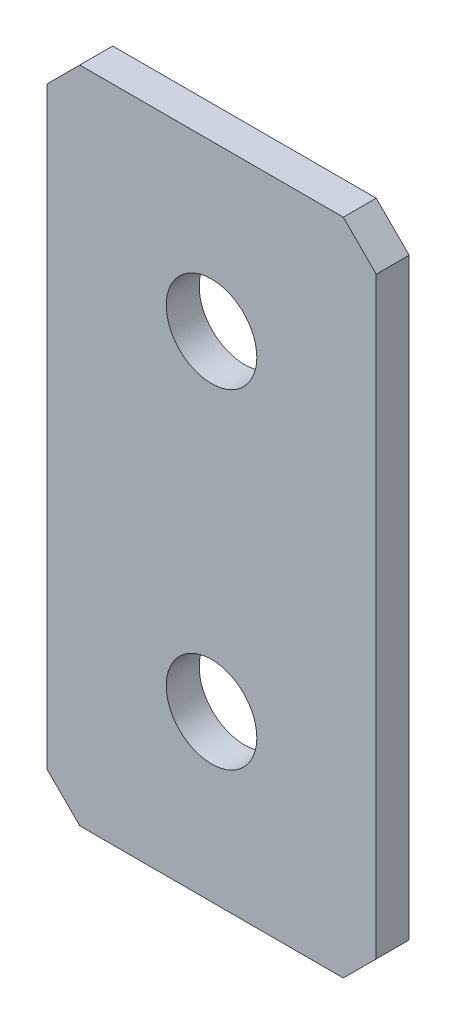
SolidWorks part; units mm, degrees
material "Простая углеродистая сталь"
ref_plane "Спереди(Плоскость XY)" through (0, 0, 0) normal (0, 0, 1) x (1, 0, 0)
ref_plane "Сверху(Плоскость XZ)" through (0, 0, 0) normal (0, 1, 0) x (1, 0, 0)
ref_plane "Справа(Плоскость ZY)" through (0, 0, 0) normal (1, 0, 0) x (0, 0, -1)
sketch "Эскиз1" plane through (0, 0, 0) normal (0, 0, 1) x (1, 0, 0)
  line L1 (-10, -20) -> (10, -20)
  line L2 (-10, -20) -> (-10, 20)
  line L3 (-10, 20) -> (10, 20)
  line L4 (10, -20) -> (10, 20)
  line L5 (-10, -20) -> (10, 20) construction
  line L6 (-10, 20) -> (10, -20) construction
  point P0 (0, 0)
  dimension "D1" = 20
  dimension "D2" = 40
extrude "Бобышка-Вытянуть1" add sketch "Эскиз1" along normal blind 2
chamfer "Фаска1" distance 2 angle 45 4 edges at (-10, -20, 1) (10, -20, 1) (-10, 20, 1) (10, 20, 1)
hole_wizard "Отверстие с зазором M51" positions "Эскиз2" profile "Эскиз3" hole size "M5" standard "DIN" end condition through all
sketch "Эскиз2" plane through (0, 0, 2) normal (0, 0, 1) x (1, 0, 0)
  line L12 (0, 20) -> (0, -20) construction
  line L13 (8, 20) -> (-8, 20) construction
  line L14 (-8, -20) -> (8, -20) construction
  point P204 (0, 30)
  point P206 (0, 10)
  point P208 (0, -10)
  point P210 (0, -30)
  dimension "D1" = 20
  dimension "D2" = 20
  dimension "D3" = 20
  dimension "D4" = 10
sketch "Эскиз3" plane through (0, -30, 2) normal (1, 0, 0) x (0, -1, 0)
  line L0 (0, 0) -> (0, 2)
  line L1 (0, 2) -> (2.75, 2)
  line L2 (2.75, 2) -> (2.75, 0)
  line L5 (2.75, 0) -> (0, 0)
  line L11 (0, -6.35) -> (0, 107.95) construction
  dimension "Диаметр сквозного отверстия" = 5.5
  dimension "Глубина сквозного отверстия" = 2
